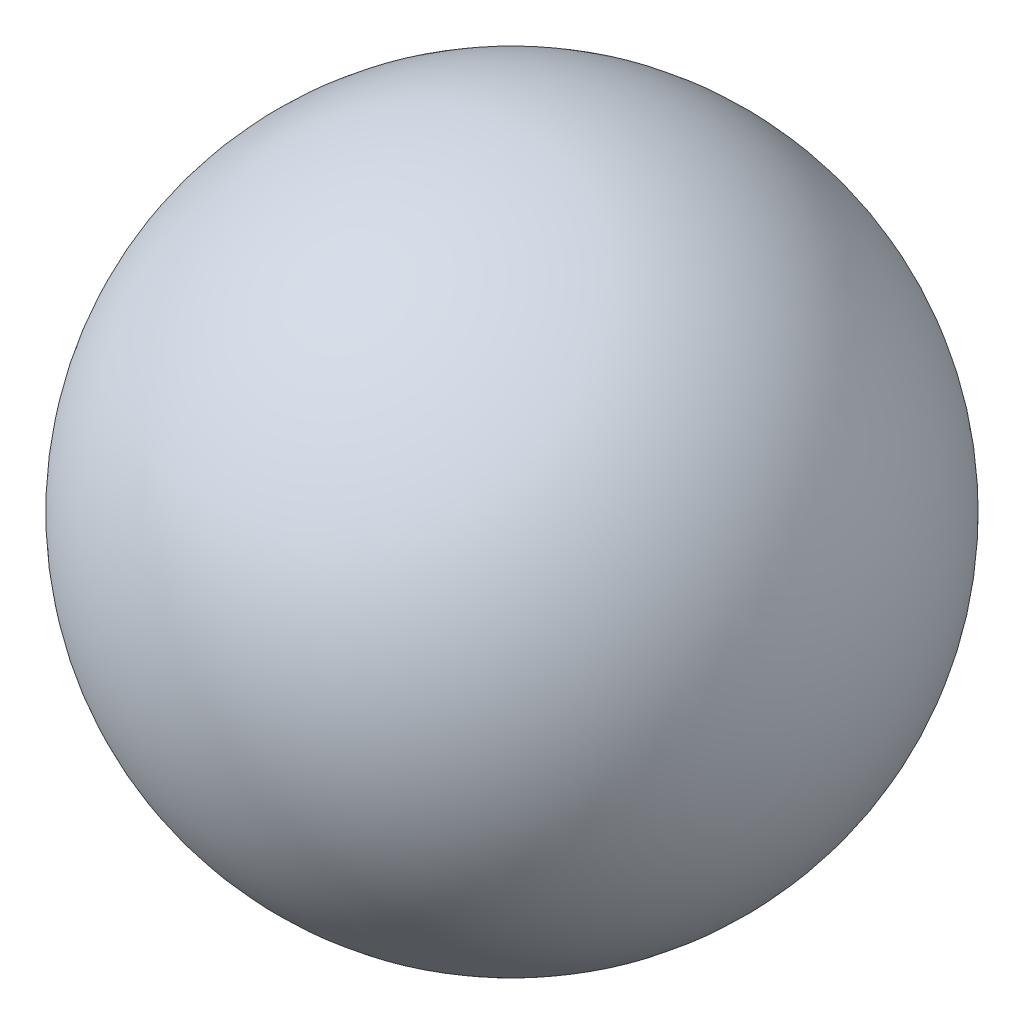
SolidWorks part; units mm, degrees
ref_plane "Спереди" through (0, 0, 0) normal (0, 0, 1) x (1, 0, 0)
ref_plane "Сверху" through (0, 0, 0) normal (0, 1, 0) x (1, 0, 0)
ref_plane "Справа" through (0, 0, 0) normal (1, 0, 0) x (0, 0, -1)
sketch "Эскиз1" plane through (0, 0, 0) normal (1, 0, 0) x (0, 0, -1)
  line L0 (0, 50) -> (0, -50) construction
  line L1 (0, 50) -> (0, -50)
  arc A0 (0, -50) -> (0, 50) centre (0, 0) ccw
  dimension "D1" = 100
revolve "Повернуть1" add sketch "Эскиз1" angle 360 about L0
